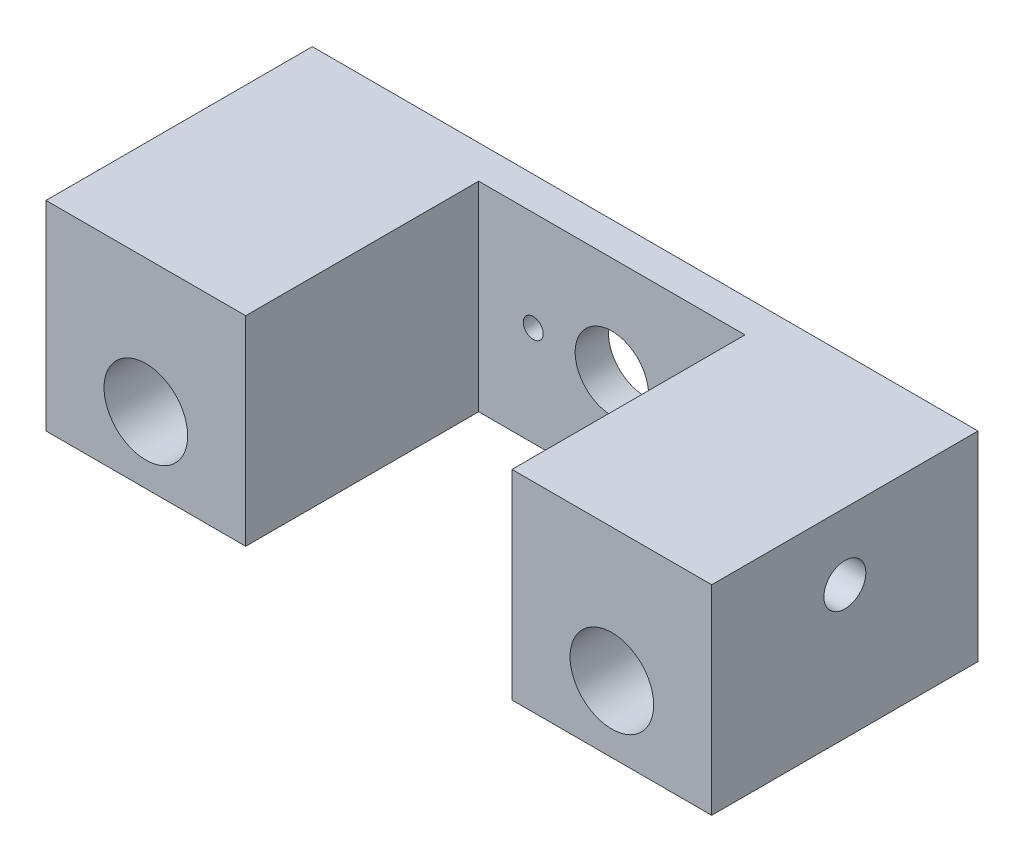
SolidWorks part; units mm, degrees
ref_plane "Front Plane" through (0, 0, 0) normal (0, 0, 1) x (1, 0, 0)
ref_plane "Top Plane" through (0, 0, 0) normal (0, 1, 0) x (1, 0, 0)
ref_plane "Right Plane" through (0, 0, 0) normal (1, 0, 0) x (0, 0, -1)
sketch "Sketch1" plane through (0, 0, 0) normal (0, 0, 1) x (1, 0, 0)
  line L0 (0, 0) -> (0, -9.525) construction
  line L1 (-31.75, 9.525) -> (31.75, 9.525)
  line L2 (-31.75, 9.525) -> (-31.75, -9.525)
  line L3 (-31.75, -9.525) -> (31.75, -9.525)
  line L4 (31.75, 9.525) -> (31.75, -9.525)
  line L5 (-31.75, 9.525) -> (31.75, -9.525) construction
  line L6 (-31.75, -9.525) -> (31.75, 9.525) construction
  line L7 (-22.225, -3.175) -> (0, -3.175) construction
  line L8 (22.225, -3.175) -> (0, -3.175) construction
  circle A1 centre (-22.225, -3.175) radius 3.9878
  circle A2 centre (22.225, -3.175) radius 3.9878
  point P0 (0, 0)
  dimension "D5" = 7.9756
  dimension "D1" = 19.05
  dimension "D2" = 63.5
  dimension "D4" = 44.45
  dimension "D6" = 6.35
extrude "Boss-Extrude1" add sketch "Sketch1" against normal blind 25.4
sketch "Sketch2" plane through (-31.75, 0, 0) normal (-1, 0, 0) x (0, 0, 1)
  line L0 (-12.7, -9.525) -> (-12.7, 9.525) construction
  line L1 (-25.4, -9.525) -> (0, -9.525) construction
  line L2 (-25.4, 9.525) -> (0, 9.525) construction
  circle A0 centre (-12.7, 3.175) radius 2
  dimension "D1" = 4
  dimension "D2" = 6.35
extrude "Cut-Extrude1" cut sketch "Sketch2" against normal blind 6.35
ref_plane "Plane1" through (0, 0, 0) normal (-1, 0, 0) x (0, 0, 1)
mirror "Mirror1" about plane through (0, 0, 0) normal (-1, 0, 0) of "Cut-Extrude1"
sketch "Sketch3" plane through (0, 0, 0) normal (0, 0, 1) x (1, 0, 0)
  line L0 (31.75, 9.525) -> (-31.75, 9.525) construction
  line L1 (-12.7, -9.525) -> (12.7, -9.525)
  line L2 (-12.7, -9.525) -> (-12.7, 9.525)
  line L3 (-12.7, 9.525) -> (12.7, 9.525)
  line L4 (12.7, -9.525) -> (12.7, 9.525)
  line L5 (-12.7, -9.525) -> (12.7, 9.525) construction
  line L6 (-12.7, 9.525) -> (12.7, -9.525) construction
  point P0 (0, 0)
  dimension "D1" = 25.4
extrude "Cut-Extrude2" cut sketch "Sketch3" against normal blind 22.225
sketch "Sketch6" plane through (0, 0, -22.225) normal (0, 0, 1) x (1, 0, 0)
  circle A1 centre (-7.5, 0) radius 0.95 construction
  circle A3 centre (7.5, 0) radius 0.95 construction
  circle A5 centre (-7.5, 0) radius 0.95
  circle A7 centre (7.5, 0) radius 0.95
  circle A8 centre (0, 0) radius 3.5 construction
  circle A9 centre (0, 0) radius 3.5
extrude "Cut-Extrude3" cut sketch "Sketch6" against normal through all
